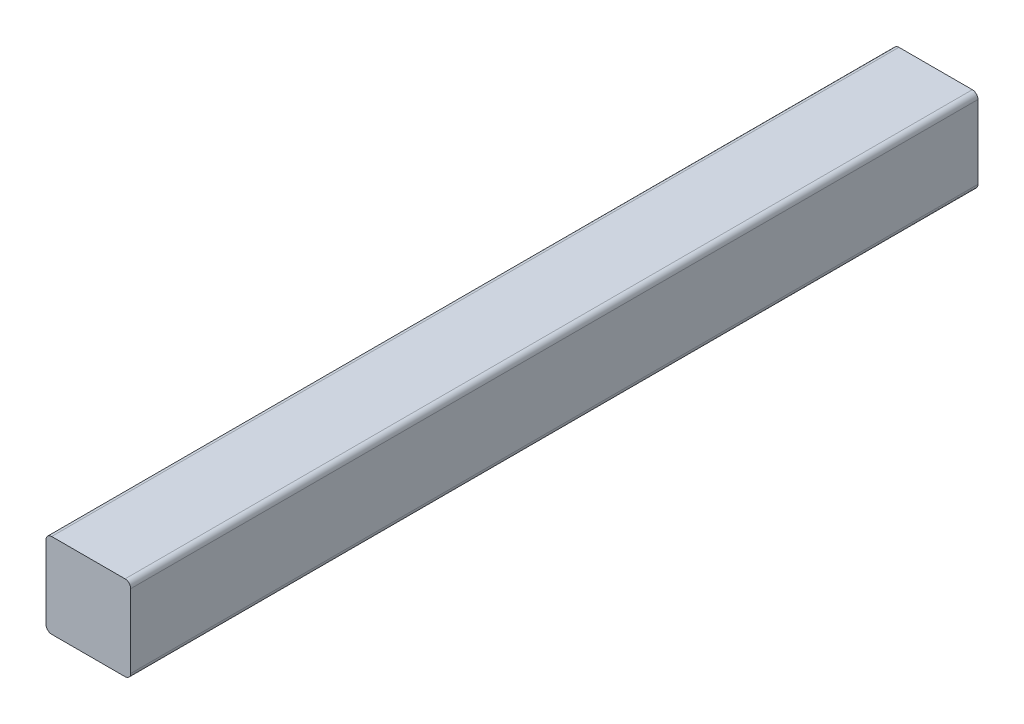
SolidWorks part; units mm, degrees
ref_plane "Front Plane" through (0, 0, 0) normal (0, 0, 1) x (1, 0, 0)
ref_plane "Top Plane" through (0, 0, 0) normal (0, 1, 0) x (1, 0, 0)
ref_plane "Right Plane" through (0, 0, 0) normal (1, 0, 0) x (0, 0, -1)
sketch "Sketch1" plane through (0, 0, 0) normal (0, 0, 1) x (1, 0, 0)
  line L0 (2, 0) -> (28, 0)
  line L1 (30, 2) -> (30, 28)
  line L2 (28, 30) -> (2, 30)
  line L3 (0, 28) -> (0, 2)
  arc A0 (2, 0) -> (0, 2) centre (2, 2) cw
  arc A1 (30, 2) -> (28, 0) centre (28, 2) cw
  arc A2 (28, 30) -> (30, 28) centre (28, 28) cw
  arc A3 (0, 28) -> (2, 30) centre (2, 28) cw
  point P7 (0, 0)
  dimension "D1" = 2
  dimension "D2" = 2
  dimension "D3" = 2
  dimension "D4" = 2
sketch "Sketch3" plane through (0, 0, 0) normal (0, 0, 1) x (1, 0, 0)
  line L0 (2, 0) -> (28, 0)
  line L1 (30, 2) -> (30, 28)
  line L2 (28, 30) -> (2, 30)
  line L3 (0, 28) -> (0, 2)
  arc A0 (2, 0) -> (0, 2) centre (2, 2) cw
  arc A1 (30, 2) -> (28, 0) centre (28, 2) cw
  arc A2 (28, 30) -> (30, 28) centre (28, 28) cw
  arc A3 (0, 28) -> (2, 30) centre (2, 28) cw
  dimension "D1" = 2
extrude "Boss-Extrude1" add sketch "Sketch3" along normal blind 300
